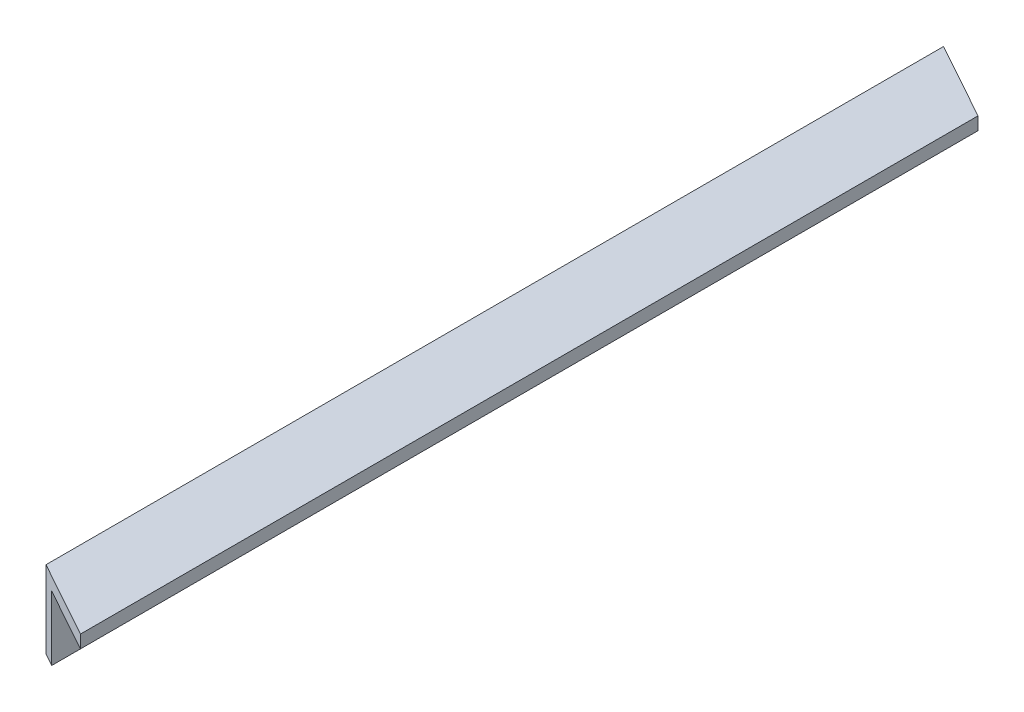
SolidWorks part; units mm, degrees
ref_plane "Front Plane" through (0, 0, 0) normal (0, 0, 1) x (1, 0, 0)
ref_plane "Top Plane" through (0, 0, 0) normal (0, 1, 0) x (1, 0, 0)
ref_plane "Right Plane" through (0, 0, 0) normal (1, 0, 0) x (0, 0, -1)
sketch "Sketch1" plane through (0, 0, 0) normal (0, 0, 1) x (1, 0, 0)
  line L0 (0, 0) -> (0, -38.1)
  line L1 (0, -38.1) -> (6.35, -38.1)
  line L2 (6.35, -38.1) -> (6.35, -6.35)
  line L3 (6.35, -6.35) -> (38.1, -6.35)
  line L4 (38.1, -6.35) -> (38.1, 0)
  line L5 (38.1, 0) -> (0, 0)
  dimension "D1" = 38.1
  dimension "D2" = 6.35
extrude "OAL Angle" add sketch "Sketch1" along normal blind 463.55
sketch "Sketch2" plane through (0, 0, 0) normal (0, 1, 0) x (1, 0, 0)
  line L0 (0, 0) -> (38.1, -21.1192)
  line L1 (38.1, -463.55) -> (38.1, 0) construction
  line L2 (38.1, -21.1192) -> (38.1, 0)
  line L3 (38.1, 0) -> (0, 0)
  line L4 (38.1, -463.55) -> (0, -442.4308)
  line L5 (0, -463.55) -> (0, 0) construction
  line L6 (0, -442.4308) -> (0, -463.55)
  line L7 (0, -463.55) -> (38.1, -463.55)
  dimension "D1" = 61
  dimension "D2" = 61
extrude "Angle Cutourt" cut sketch "Sketch2" against normal through all
